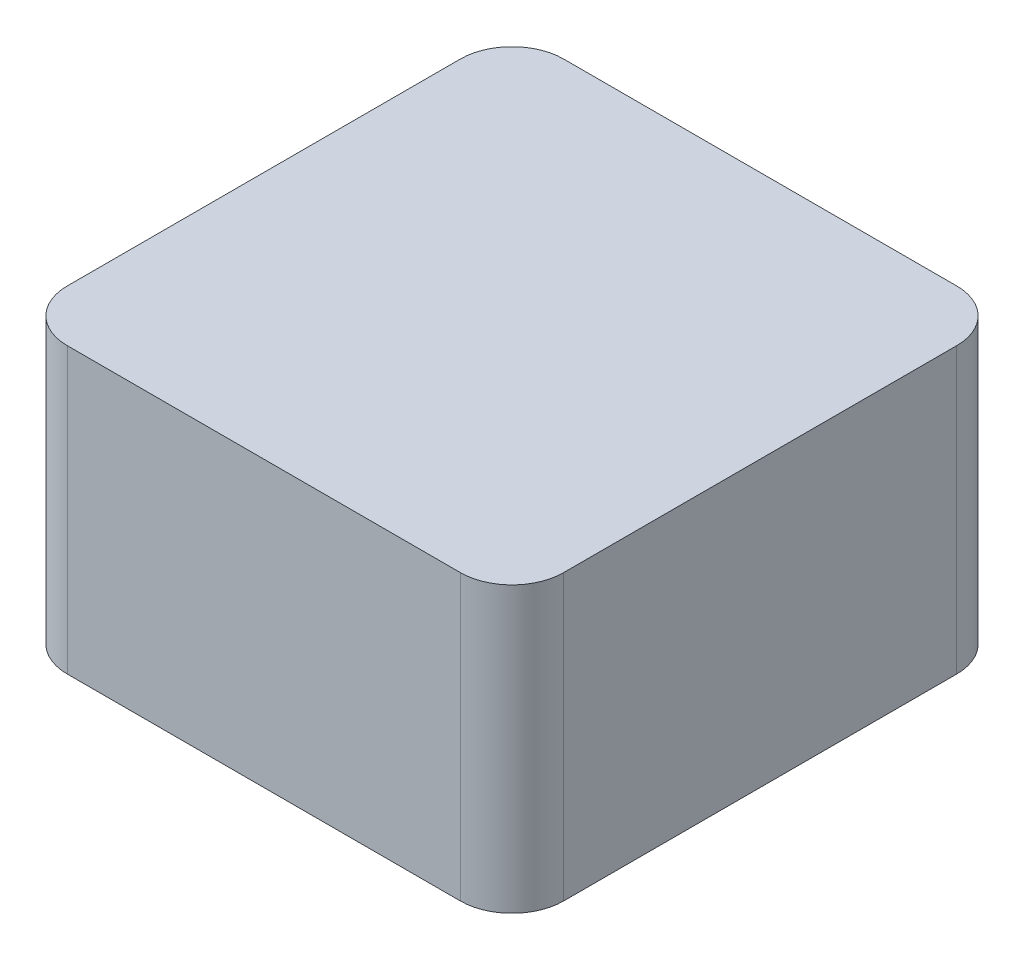
SolidWorks part; units mm, degrees
ref_plane "Front Plane" through (0, 0, 0) normal (0, 0, 1) x (1, 0, 0)
ref_plane "Top Plane" through (0, 0, 0) normal (0, 1, 0) x (1, 0, 0)
ref_plane "Right Plane" through (0, 0, 0) normal (1, 0, 0) x (0, 0, -1)
sketch "Sketch1" plane through (0, 0, 0) normal (0, 1, 0) x (1, 0, 0)
  line L1 (-9.4853, 9.9566) -> (28.9147, 9.9566)
  line L2 (-9.4853, 9.9566) -> (-9.4853, -28.4434)
  line L3 (-9.4853, -28.4434) -> (28.9147, -28.4434)
  line L4 (28.9147, 9.9566) -> (28.9147, -28.4434)
  line L5 (9.7147, -28.4434) -> (9.7147, 9.9566) construction
  line L6 (-9.4853, -9.2434) -> (28.9147, -9.2434) construction
  point P188 (9.7147, -9.2434)
  dimension "D1" = 38.4
sketch "Sketch2" plane through (0, 0, 0) normal (0, 1, 0) x (1, 0, 0)
  line L0 (-9.4853, 9.9566) -> (28.9147, 9.9566)
  line L1 (-9.4853, 9.9566) -> (-9.4853, -28.4434)
  line L2 (-9.4853, -28.4434) -> (28.9147, -28.4434)
  line L3 (28.9147, 9.9566) -> (28.9147, -28.4434)
  line L4 (9.7147, -28.4434) -> (9.7147, 9.9566) construction
  line L5 (-9.4853, -9.2434) -> (28.9147, -9.2434) construction
  point P8 (9.7147, -9.2434)
extrude "Boss-Extrude1" add sketch "Sketch2" along normal blind 22
fillet "Fillet1" radius 4 4 edges at (-9.4853, 11, -9.9566) (28.9147, 11, -9.9566) (28.9147, 11, 28.4434) (-9.4853, 11, 28.4434)
